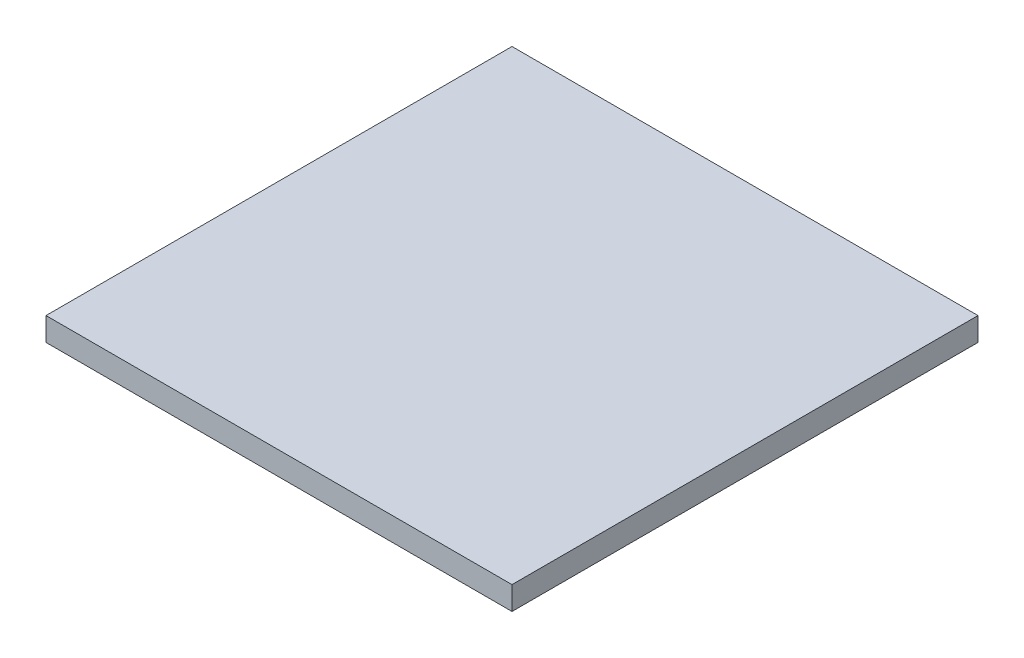
SolidWorks part; units mm, degrees
ref_plane "Front Plane" through (0, 0, 0) normal (0, 0, 1) x (1, 0, 0)
ref_plane "Top Plane" through (0, 0, 0) normal (0, 1, 0) x (1, 0, 0)
ref_plane "Right Plane" through (0, 0, 0) normal (1, 0, 0) x (0, 0, -1)
sketch "Sketch1" plane through (0, 0, 0) normal (0, 1, 0) x (1, 0, 0)
  line L1 (0, 0) -> (20, 0)
  line L2 (0, 0) -> (0, 20)
  line L3 (0, 20) -> (20, 20)
  line L4 (20, 0) -> (20, 20)
  dimension "D1" = 20
  dimension "D2" = 20
extrude "Boss-Extrude1" add sketch "Sketch1" along normal blind 1
